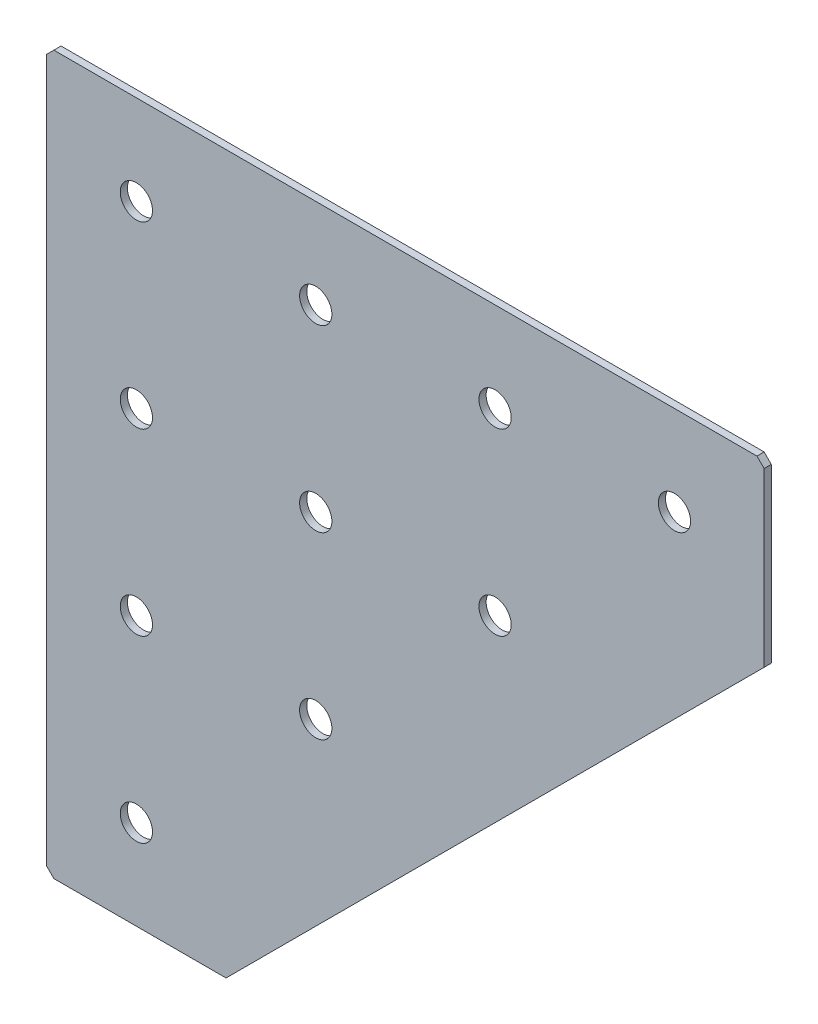
SolidWorks part; units mm, degrees
ref_plane "Спереди" through (0, 0, 0) normal (0, 0, 1) x (1, 0, 0)
ref_plane "Сверху" through (0, 0, 0) normal (0, 1, 0) x (1, 0, 0)
ref_plane "Справа" through (0, 0, 0) normal (1, 0, 0) x (0, 0, -1)
sketch "Эскиз1" plane through (0, 0, 0) normal (0, 0, 1) x (1, 0, 0)
  line L0 (0, 0) -> (0, -200)
  line L1 (0, 0) -> (200, 0)
  line L2 (200, 0) -> (200, -50)
  line L3 (0, -200) -> (50, -200)
  line L4 (200, -50) -> (50, -200)
  dimension "D1" = 200
  dimension "D2" = 50
extrude "Бобышка-Вытянуть1" add sketch "Эскиз1" along normal blind 2
chamfer "Фаска1" distance 2 angle 45 3 edges at (0, -200, 1) (0, 0, 1) (200, 0, 1)
hole_wizard "Отверстие с зазором M81" positions "Эскиз6" profile "Эскиз7" hole size "M8" standard "DIN" end condition through all
sketch "Эскиз6" plane through (0, 0, 2) normal (0, 0, 1) x (1, 0, 0)
  line L0 (25, -25) -> (75, -25) construction
  line L1 (75, -25) -> (125, -25) construction
  line L2 (125, -25) -> (175, -25) construction
  line L4 (25, -25) -> (25, -75) construction
  line L5 (25, -75) -> (25, -125) construction
  line L6 (25, -125) -> (25, -175) construction
  line L8 (25, -25) -> (0, -25) construction
  line L9 (0, -2) -> (0, -198) construction
  line L11 (25, -25) -> (25, 0) construction
  line L12 (198, 0) -> (2, 0) construction
  line L13 (25, -75) -> (75, -75) construction
  point P0 (25, -25)
  point P2 (75, -25)
  point P4 (125, -25)
  point P6 (175, -25)
  point P8 (25, -75)
  point P10 (25, -125)
  point P12 (25, -175)
  point P16 (75, -125)
  point P18 (125, -75)
  point P56 (75, -75)
  dimension "D1" = 25
  dimension "D2" = 50
sketch "Эскиз7" plane through (25, -25, 2) normal (1, 0, 0) x (0, -1, 0)
  line L0 (0, 0) -> (0, 2)
  line L1 (0, 2) -> (4.5, 2)
  line L2 (4.5, 2) -> (4.5, 0)
  line L5 (4.5, 0) -> (0, 0)
  line L11 (0, -6.35) -> (0, 107.95) construction
  dimension "Диаметр сквозного отверстия" = 9
  dimension "Глубина сквозного отверстия" = 2
